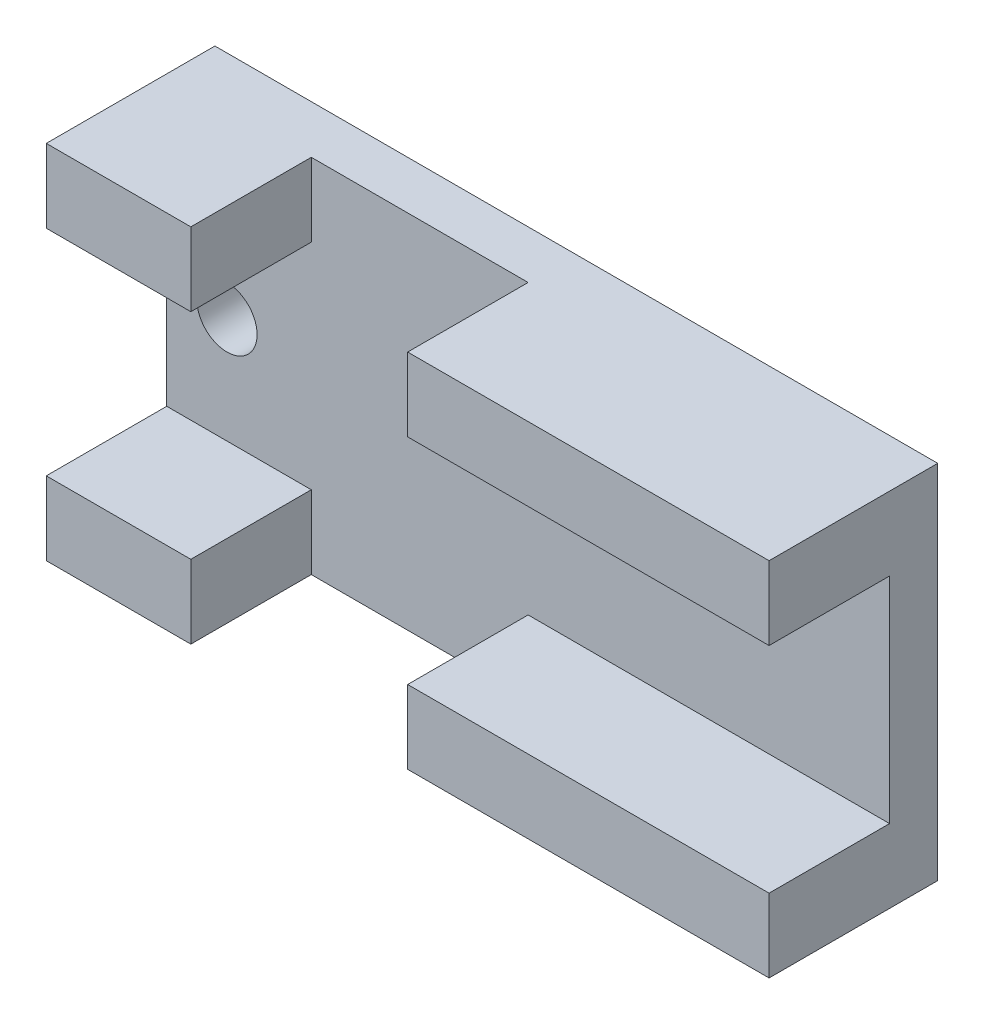
SolidWorks part; units mm, degrees
ref_plane "Front Plane" through (0, 0, 0) normal (0, 0, 1) x (1, 0, 0)
ref_plane "Top Plane" through (0, 0, 0) normal (0, 1, 0) x (1, 0, 0)
ref_plane "Right Plane" through (0, 0, 0) normal (1, 0, 0) x (0, 0, -1)
sketch "Sketch1" plane through (0, 0, 0) normal (0, 0, 1) x (1, 0, 0)
  line L1 (-38.1, -19.05) -> (38.1, -19.05)
  line L2 (-38.1, -19.05) -> (-38.1, 19.05)
  line L3 (-38.1, 19.05) -> (38.1, 19.05)
  line L4 (38.1, -19.05) -> (38.1, 19.05)
  line L5 (-38.1, -19.05) -> (38.1, 19.05) construction
  line L6 (-38.1, 19.05) -> (38.1, -19.05) construction
  point P0 (0, 0)
  dimension "D1" = 76.2
  dimension "D2" = 38.1
extrude "Boss-Extrude1" add sketch "Sketch1" along normal blind 5.08
sketch "Sketch2" plane through (0, 0, 5.08) normal (0, 0, 1) x (1, 0, 0)
  line L0 (38.1, 19.05) -> (-38.1, 19.05) construction
  line L1 (0, 19.05) -> (38.1, 19.05)
  line L2 (0, 19.05) -> (0, 11.303)
  line L3 (0, 11.303) -> (38.1, 11.303)
  line L4 (38.1, 19.05) -> (38.1, 11.303)
  line L5 (38.1, -19.05) -> (38.1, 19.05) construction
  line L6 (-38.1, -19.05) -> (38.1, -19.05) construction
  line L7 (0, -19.05) -> (38.1, -19.05)
  line L8 (0, -19.05) -> (0, -11.303)
  line L9 (0, -11.303) -> (38.1, -11.303)
  line L10 (38.1, -19.05) -> (38.1, -11.303)
  line L12 (-38.1, 19.05) -> (-22.86, 19.05)
  line L13 (-38.1, 19.05) -> (-38.1, 11.303)
  line L14 (-38.1, 11.303) -> (-22.86, 11.303)
  line L15 (-22.86, 19.05) -> (-22.86, 11.303)
  line L16 (-38.1, -19.05) -> (-22.86, -19.05)
  line L17 (-38.1, -19.05) -> (-38.1, -11.303)
  line L18 (-38.1, -11.303) -> (-22.86, -11.303)
  line L19 (-22.86, -19.05) -> (-22.86, -11.303)
  dimension "D1" = 22.606
  dimension "D2" = 38.1
  dimension "D3" = 15.24
extrude "Boss-Extrude2" add sketch "Sketch2" along normal blind 12.7
sketch "Sketch3" plane through (0, 0, 5.08) normal (0, 0, 1) x (1, 0, 0)
  line L0 (38.1, -11.303) -> (38.1, 11.303) construction
  line L2 (38.1, 19.05) -> (0, 19.05) construction
  circle A0 centre (25.4, 6.35) radius 3.175
  point P2 (0, 0)
  dimension "D1" = 6.35
  dimension "D2" = 12.7
  dimension "D3" = 12.7
extrude "Cut-Extrude1" cut sketch "Sketch3" against normal through all
sketch "Sketch4" plane through (0, 0, 5.08) normal (0, 0, 1) x (1, 0, 0)
  line L0 (-38.1, 11.303) -> (-38.1, -11.303) construction
  circle A0 centre (-31.75, 0) radius 3.175
  point P2 (0, 0)
  dimension "D1" = 6.35
  dimension "D2" = 6.35
extrude "Cut-Extrude2" cut sketch "Sketch4" against normal through all
